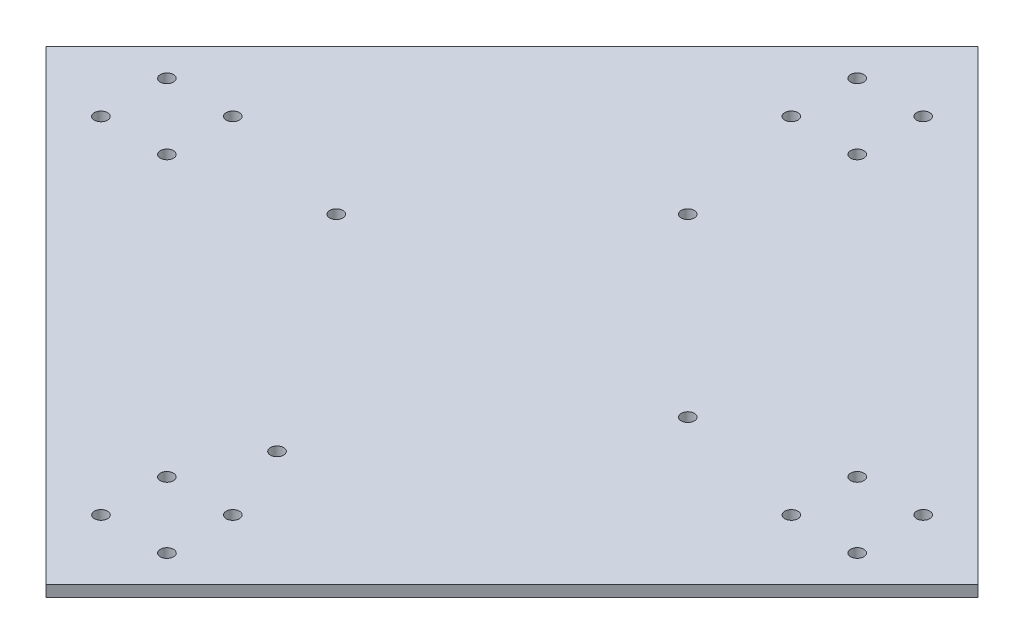
SolidWorks part; units mm, degrees
ref_plane "Front Plane" through (0, 0, 0) normal (0, 0, 1) x (1, 0, 0)
ref_plane "Top Plane" through (0, 0, 0) normal (0, 1, 0) x (1, 0, 0)
ref_plane "Right Plane" through (0, 0, 0) normal (1, 0, 0) x (0, 0, -1)
sketch "Sketch3" plane through (0, 0, 0) normal (0, 1, 0) x (1, 0, 0)
  line L0 (-20787.2475, 82043.6963) -> (260209.1191, 82043.6963) construction
  line L1 (-11608.6225, 82043.6963) -> (94457.3926, 188109.7135)
  line L2 (-11608.6225, 82043.6963) -> (94472.1693, -24037.0955)
  line L3 (94472.1693, -24037.0955) -> (200523.4098, 82043.6963)
  line L4 (94457.3926, 188109.7135) -> (200523.4098, 82043.6963)
  line L5 (94472.1693, 212458.6987) -> (94472.1693, -55401.6589) construction
  line L6 (31440.0954, 168109.7135) -> (166638.0807, 168109.7135) construction
  line L7 (31440.0954, 153109.7135) -> (166638.0807, 153109.7135) construction
  line L8 (86972.1693, 173134.9572) -> (86972.1693, 141299.0948) construction
  line L9 (101972.1693, 173134.9572) -> (101972.1693, 141299.0948) construction
  circle A0 centre (86957.3947, 168109.7135) radius 1500
  circle A1 centre (101972.1693, 168109.7135) radius 1500
  circle A2 centre (101972.1693, 153109.7135) radius 1500
  circle A3 centre (86972.1693, 153109.7135) radius 1500
  circle A4 centre (165538.1865, 74543.6963) radius 1500
  circle A5 centre (86972.1693, 10977.6792) radius 1500
  circle A6 centre (23406.1521, 89543.6963) radius 1500
  circle A7 centre (180538.1865, 89558.4709) radius 1500
  circle A8 centre (180538.1865, 74543.6963) radius 1500
  circle A9 centre (165538.1865, 74543.6963) radius 1500
  circle A10 centre (165538.1865, 89543.6963) radius 1500
  circle A11 centre (101986.9439, -4022.3208) radius 1500
  circle A12 centre (86972.1693, -4022.3208) radius 1500
  circle A13 centre (86972.1693, 10977.6792) radius 1500
  circle A14 centre (101972.1693, 10977.6792) radius 1500
  circle A15 centre (8406.1521, 74528.9217) radius 1500
  circle A16 centre (8406.1521, 89543.6963) radius 1500
  circle A17 centre (23406.1521, 89543.6963) radius 1500
  circle A18 centre (23406.1521, 74543.6963) radius 1500
  point P33 (94472.1693, 82043.6963)
  point P58 (94472.1693, 82043.6963)
  dimension "D11" = 3000
  dimension "D12" = 3000
  dimension "D13" = 3000
  dimension "D14" = 3000
  dimension "D1" = 150000
  dimension "D2" = 150000
  dimension "D3" = 135197.9853
  dimension "D4" = 135197.9853
  dimension "D5" = 280996.3666
  dimension "D6" = 267860.3576
  dimension "D7" = 15000
  dimension "D8" = 20000
  dimension "D9" = 7500
  dimension "D10" = 7500
  dimension "D15" = 4
  dimension "D16" = 4
extrude "Boss-Extrude2" add sketch "Sketch3" along normal blind 2500 contours L4 L1 L2 L3 A18 A16 A15 A14 A12 A11 A10 A8 A7 A6 A5 A4 A3 A2 A1 A0
sketch "Sketch4" plane through (0, 2500, 0) normal (0, 1, 0) x (1, 0, 0)
  line L0 (94457.3926, 188109.7135) -> (94472.1693, -24037.0955) construction
  line L1 (-11608.6225, 82043.6963) -> (200523.4098, 82043.6963) construction
  line L2 (134464.697, 107393.7963) -> (134464.697, 59093.3047) construction
  line L3 (65557.9082, 122043.6963) -> (118820.7791, 122043.6963) construction
  line L4 (54464.697, 110227.9456) -> (54464.697, 56621.0621) construction
  line L5 (77943.3057, 42043.6963) -> (114552.8846, 42043.6963) construction
  circle A0 centre (94461.9943, 122043.6963) radius 1500
  circle A1 centre (134464.697, 82043.6963) radius 1500
  circle A2 centre (94468.5067, 28546.6094) radius 1500
  circle A3 centre (54464.697, 82043.6963) radius 1500
  point P10 (134464.697, 83243.5505)
  point P25 (0, 0)
  dimension "D5" = 3000
  dimension "D6" = 3000
  dimension "D7" = 3000
  dimension "D8" = 3000
  dimension "D1" = 40000
  dimension "D2" = 40000
  dimension "D3" = 80000
  dimension "D4" = 80000
extrude "Cut-Extrude4" cut sketch "Sketch4" against normal blind 5000 contours A2 | A3 | A0 | A1
scale "Scale1" scale about centroid uniform scaling yes scale factor 0.001
